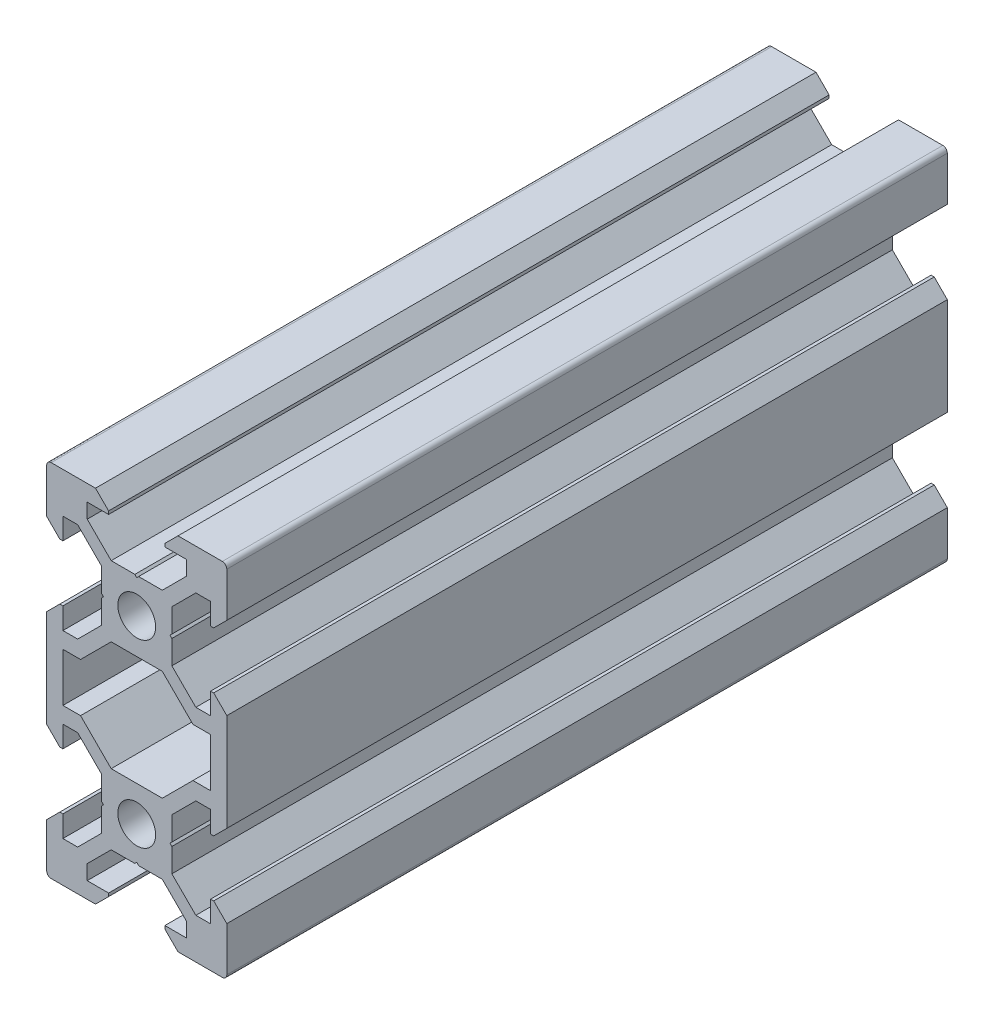
SolidWorks part; units mm, degrees
material "6061-T6 (SS)"
ref_plane "Front Plane" through (0, 0, 0) normal (0, 0, 1) x (1, 0, 0)
ref_plane "Top Plane" through (0, 0, 0) normal (0, 1, 0) x (1, 0, 0)
ref_plane "Right Plane" through (0, 0, 0) normal (1, 0, 0) x (0, 0, -1)
sketch "Sketch1" plane through (0, 0, 0) normal (0, 0, 1) x (1, 0, 0)
  line L0 (0, 0) -> (10, 0) construction
  line L1 (9.5, -20) -> (-9.5, -20)
  line L2 (10, -19.5) -> (10, 19.5)
  line L3 (9.5, 20) -> (-9.5, 20)
  line L4 (-10, -19.5) -> (-10, 19.5)
  line L5 (10, -20) -> (-10, 20) construction
  line L6 (10, 20) -> (-10, -20) construction
  circle A0 centre (0, 10) radius 2.1
  circle A1 centre (0, -10) radius 2.1
  arc A2 (-9.5, -20) -> (-10, -19.5) centre (-9.5, -19.5) cw
  arc A3 (9.5, -20) -> (10, -19.5) centre (9.5, -19.5) ccw
  arc A4 (10, 19.5) -> (9.5, 20) centre (9.5, 19.5) ccw
  arc A5 (-9.5, 20) -> (-10, 19.5) centre (-9.5, 19.5) ccw
  point P0 (0, 0)
  line B0 (0, 10) -> (0, 20) construction
  line B1 (0, 13.69) -> (-0.21, 13.9)
  line B2 (-0.21, 13.9) -> (-2.8393, 13.9)
  line B3 (-2.8393, 13.9) -> (-5.5, 16.5607)
  line B4 (-5.5, 16.5607) -> (-5.5, 18.2)
  line B5 (-5.5, 18.2) -> (-3.125, 18.2)
  line B6 (-3.125, 18.2) -> (-3.125, 18.545)
  line B7 (-3.125, 18.545) -> (-4.58, 20)
  line B8 (-4.58, 20) -> (4.58, 20)
  line B9 (0, 10) -> (-5.9132, 15.9132) construction
  line B10 (3.125, 18.545) -> (4.58, 20)
  line B11 (3.125, 18.2) -> (3.125, 18.545)
  line B12 (5.5, 18.2) -> (3.125, 18.2)
  line B13 (5.5, 16.5607) -> (5.5, 18.2)
  line B14 (2.8393, 13.9) -> (5.5, 16.5607)
  line B15 (0.21, 13.9) -> (2.8393, 13.9)
  line B16 (0, 13.69) -> (0.21, 13.9)
  line B17 (0, 10) -> (-10, 10) construction
  line B18 (-3.69, 10) -> (-3.9, 9.79)
  line B19 (-3.9, 9.79) -> (-3.9, 7.1607)
  line B20 (-3.9, 7.1607) -> (-6.5607, 4.5)
  line B21 (-6.5607, 4.5) -> (-8.2, 4.5)
  line B22 (-8.2, 4.5) -> (-8.2, 6.875)
  line B23 (-8.2, 6.875) -> (-8.545, 6.875)
  line B24 (-8.545, 6.875) -> (-10, 5.42)
  line B25 (-10, 5.42) -> (-10, 14.58)
  line B26 (0, 10) -> (-5.9132, 4.0868) construction
  line B27 (-8.545, 13.125) -> (-10, 14.58)
  line B28 (-8.2, 13.125) -> (-8.545, 13.125)
  line B29 (-8.2, 15.5) -> (-8.2, 13.125)
  line B30 (-6.5607, 15.5) -> (-8.2, 15.5)
  line B31 (-3.9, 12.8393) -> (-6.5607, 15.5)
  line B32 (-3.9, 10.21) -> (-3.9, 12.8393)
  line B33 (-3.69, 10) -> (-3.9, 10.21)
  line B34 (0, -10) -> (-10, -10) construction
  line B35 (-3.69, -10) -> (-3.9, -10.21)
  line B36 (-3.9, -10.21) -> (-3.9, -12.8393)
  line B37 (-3.9, -12.8393) -> (-6.5607, -15.5)
  line B38 (-6.5607, -15.5) -> (-8.2, -15.5)
  line B39 (-8.2, -15.5) -> (-8.2, -13.125)
  line B40 (-8.2, -13.125) -> (-8.545, -13.125)
  line B41 (-8.545, -13.125) -> (-10, -14.58)
  line B42 (-10, -14.58) -> (-10, -5.42)
  line B43 (0, -10) -> (-5.9132, -15.9132) construction
  line B44 (-8.545, -6.875) -> (-10, -5.42)
  line B45 (-8.2, -6.875) -> (-8.545, -6.875)
  line B46 (-8.2, -4.5) -> (-8.2, -6.875)
  line B47 (-6.5607, -4.5) -> (-8.2, -4.5)
  line B48 (-3.9, -7.1607) -> (-6.5607, -4.5)
  line B49 (-3.9, -9.79) -> (-3.9, -7.1607)
  line B50 (-3.69, -10) -> (-3.9, -9.79)
  line B51 (0, -10) -> (0, -20) construction
  line B52 (0, -13.69) -> (0.21, -13.9)
  line B53 (0.21, -13.9) -> (2.8393, -13.9)
  line B54 (2.8393, -13.9) -> (5.5, -16.5607)
  line B55 (5.5, -16.5607) -> (5.5, -18.2)
  line B56 (5.5, -18.2) -> (3.125, -18.2)
  line B57 (3.125, -18.2) -> (3.125, -18.545)
  line B58 (3.125, -18.545) -> (4.58, -20)
  line B59 (4.58, -20) -> (-4.58, -20)
  line B60 (0, -10) -> (5.9132, -15.9132) construction
  line B61 (-3.125, -18.545) -> (-4.58, -20)
  line B62 (-3.125, -18.2) -> (-3.125, -18.545)
  line B63 (-5.5, -18.2) -> (-3.125, -18.2)
  line B64 (-5.5, -16.5607) -> (-5.5, -18.2)
  line B65 (-2.8393, -13.9) -> (-5.5, -16.5607)
  line B66 (-0.21, -13.9) -> (-2.8393, -13.9)
  line B67 (0, -13.69) -> (-0.21, -13.9)
  line B68 (0, -10) -> (10, -10) construction
  line B69 (3.69, -10) -> (3.9, -9.79)
  line B70 (3.9, -9.79) -> (3.9, -7.1607)
  line B71 (3.9, -7.1607) -> (6.5607, -4.5)
  line B72 (6.5607, -4.5) -> (8.2, -4.5)
  line B73 (8.2, -4.5) -> (8.2, -6.875)
  line B74 (8.2, -6.875) -> (8.545, -6.875)
  line B75 (8.545, -6.875) -> (10, -5.42)
  line B76 (10, -5.42) -> (10, -14.58)
  line B77 (0, -10) -> (5.9132, -4.0868) construction
  line B78 (8.545, -13.125) -> (10, -14.58)
  line B79 (8.2, -13.125) -> (8.545, -13.125)
  line B80 (8.2, -15.5) -> (8.2, -13.125)
  line B81 (6.5607, -15.5) -> (8.2, -15.5)
  line B82 (3.9, -12.8393) -> (6.5607, -15.5)
  line B83 (3.9, -10.21) -> (3.9, -12.8393)
  line B84 (3.69, -10) -> (3.9, -10.21)
  line B85 (0, 10) -> (10, 10) construction
  line B86 (3.69, 10) -> (3.9, 10.21)
  line B87 (3.9, 10.21) -> (3.9, 12.8393)
  line B88 (3.9, 12.8393) -> (6.5607, 15.5)
  line B89 (6.5607, 15.5) -> (8.2, 15.5)
  line B90 (8.2, 15.5) -> (8.2, 13.125)
  line B91 (8.2, 13.125) -> (8.545, 13.125)
  line B92 (8.545, 13.125) -> (10, 14.58)
  line B93 (10, 14.58) -> (10, 5.42)
  line B94 (0, 10) -> (5.9132, 15.9132) construction
  line B95 (8.545, 6.875) -> (10, 5.42)
  line B96 (8.2, 6.875) -> (8.545, 6.875)
  line B97 (8.2, 4.5) -> (8.2, 6.875)
  line B98 (6.5607, 4.5) -> (8.2, 4.5)
  line B99 (3.9, 7.1607) -> (6.5607, 4.5)
  line B100 (3.9, 9.79) -> (3.9, 7.1607)
  line B101 (3.69, 10) -> (3.9, 9.79)
  line B102 (-8.2, -2.7) -> (-8.2, 2.7)
  line B103 (-8.2, 2.7) -> (-6.2393, 2.7)
  line B104 (-6.2393, 2.7) -> (-2.8393, 6.1)
  line B105 (-2.8393, 6.1) -> (2.8393, 6.1)
  line B106 (0, 6.1) -> (0, 0) construction
  line B107 (0, 0) -> (-8.2, 0) construction
  line B108 (6.2393, 2.7) -> (2.8393, 6.1)
  line B109 (8.2, 2.7) -> (6.2393, 2.7)
  line B110 (8.2, -2.7) -> (8.2, 2.7)
  line B111 (8.2, -2.7) -> (6.2393, -2.7)
  line B112 (6.2393, -2.7) -> (2.8393, -6.1)
  line B113 (-2.8393, -6.1) -> (2.8393, -6.1)
  line B114 (-6.2393, -2.7) -> (-2.8393, -6.1)
  line B115 (-8.2, -2.7) -> (-6.2393, -2.7)
  line B116 (0, 6.1) -> (0, 10) construction
  line B117 (0, 10) -> (-5.0927, 4.9073) construction
  dimension "D4" = 4.2
  dimension "D5" = 0.5
  dimension "D1" = 20
  dimension "D2" = 40
  dimension "D3" = 20
sketch_block_instance "V Slot 1-4"
sketch_block "V Slot 1" parameters "D1"=10, "D2"=11, "D3"=4.3, "D4"=1.8, "D5"=0.21, "D6"=45, "D7"=9.16, "D8"=1.5, "D9"=6.25
sketch_block_instance "V Slot 1-5"
sketch_block_instance "V Slot 1-6"
sketch_block_instance "V Slot 1-7"
sketch_block_instance "V Slot 1-8"
sketch_block_instance "V Slot 1-9"
sketch_block_instance "Center Cutout 1-1"
sketch_block "Center Cutout 1" parameters "D1"=5.4, "D2"=12.2, "D3"=8.2, "D4"=45, "D5"=10, "D6"=1.5
extrude "Boss-Extrude1" add sketch "Sketch1" along normal blind 80 contours B101 B86 B87 B88 B89 B90 B91 B92 L2 A4 L3 B10 B11 B12 B13 B14 B15 B16 B1 B2 B3 B4 B5 B6 B7 A5 L4 B27 B28 B29 B30 B31 B32 B33 B18 B19 B20 B21 B22 B23 B24 B44 B45 B46 B47 B48 B49 B50 B35
ref_plane "Plane1" through (0, 0, 40) normal (0, 0, 1) x (1, 0, 0)
